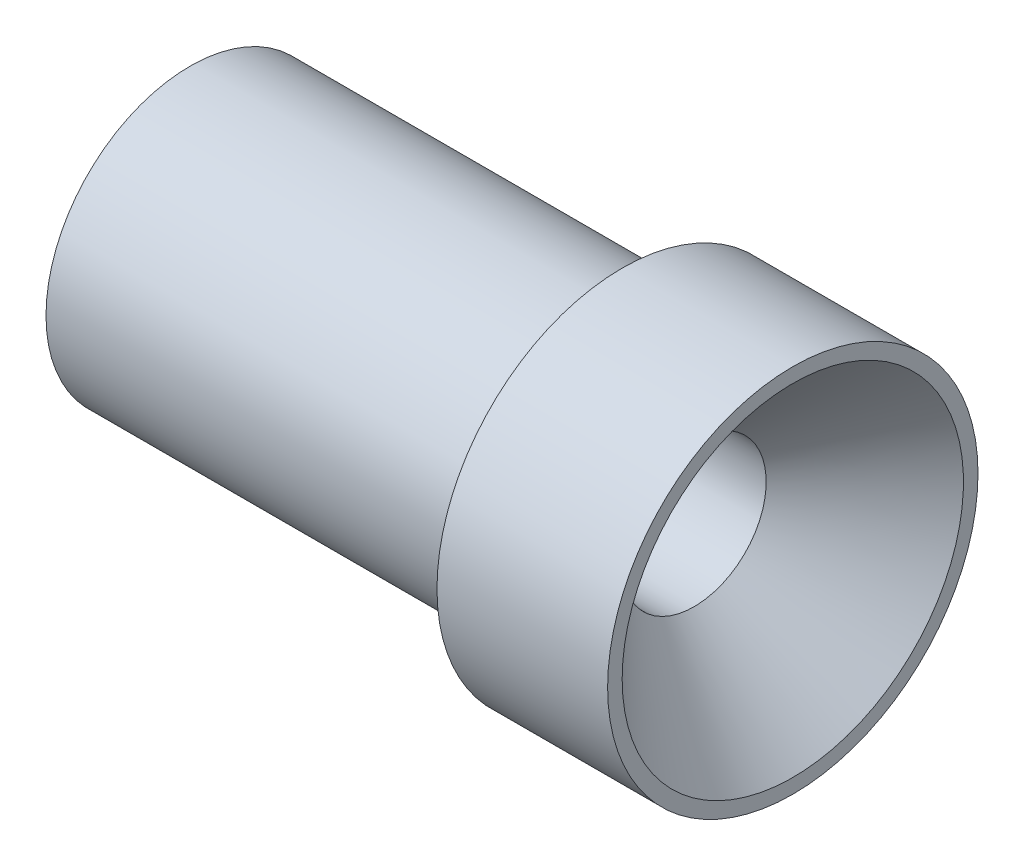
SolidWorks part; units mm, degrees
ref_plane "Ön Düzlem" through (0, 0, 0) normal (0, 0, 1) x (1, 0, 0)
ref_plane "Üst Düzlem" through (0, 0, 0) normal (0, 1, 0) x (1, 0, 0)
ref_plane "Sağ Düzlem" through (0, 0, 0) normal (1, 0, 0) x (0, 0, -1)
sketch "Çizim1" plane through (0, 0, 0) normal (0, 0, 1) x (1, 0, 0)
  line L0 (0, 0) -> (20.1515, 0) construction
  line L1 (15, 4.5) -> (10.5, 4.5)
  line L2 (15, 4.5) -> (12.25, 1.75)
  line L3 (0, 1.75) -> (0, 3.5)
  line L4 (12.25, 1.75) -> (0, 1.75)
  line L5 (0, 3.5) -> (10.5, 3.5)
  line L6 (10.5, 3.5) -> (10.5, 4.5)
  point P2 (0, 0)
  point P5 (-1.7343, 1.7364)
  point P10 (0, 0)
  point P12 (0, 0)
  point P13 (-3.0509, 1.6652)
  point P14 (-3.0331, 2.5014)
  point P16 (0, 0)
  point P17 (0, 1.75)
  dimension "D1" = 1.75
  dimension "D2" = 4.5
  dimension "D3" = 15
  dimension "D4" = 4.5
  dimension "D5" = 45
  dimension "D6" = 3.5
revolve "Döndür1" add sketch "Çizim1" angle 360 about L0
chamfer "Pah1" distance 0.5 angle 45 1 edges at (15, 0, 4.5)
